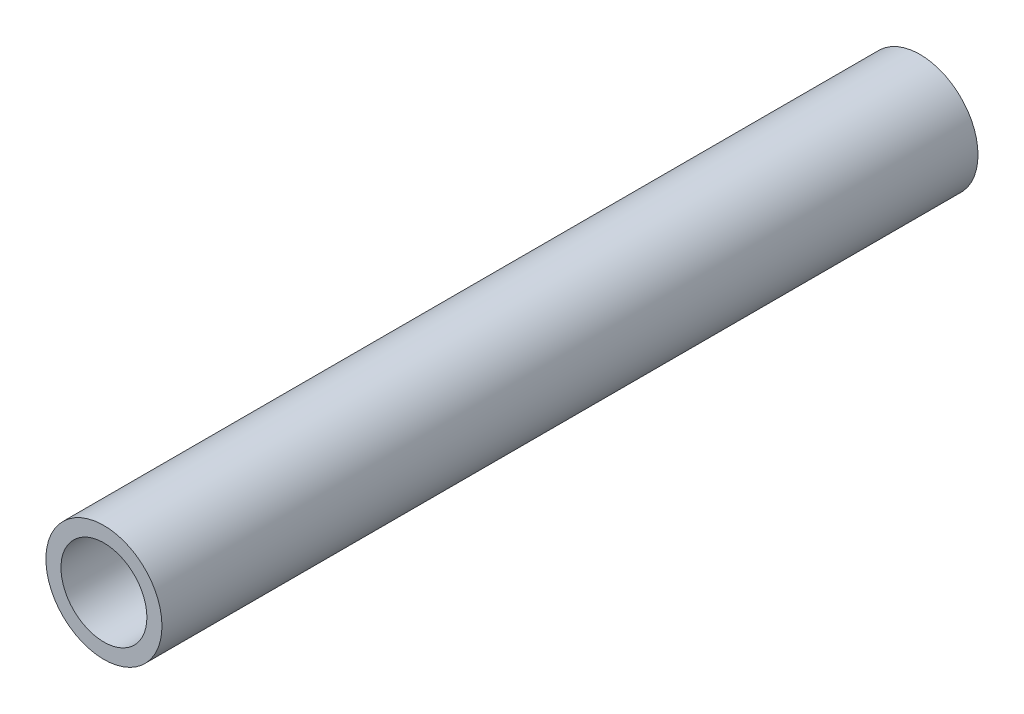
SolidWorks part; units mm, degrees
ref_plane "Front Plane" through (0, 0, 0) normal (0, 0, 1) x (1, 0, 0)
ref_plane "Top Plane" through (0, 0, 0) normal (0, 1, 0) x (1, 0, 0)
ref_plane "Right Plane" through (0, 0, 0) normal (1, 0, 0) x (0, 0, -1)
sketch "Sketch1" plane through (0, 0, 0) normal (0, 0, 1) x (1, 0, 0)
  circle A0 centre (0, 0) radius 10.668
  dimension "Pipe OD" = 21.336
extrude "Extrude-Thin1" add sketch "Sketch1" along normal mid plane 150 thin thin type one direction reverse wall 2.7686
